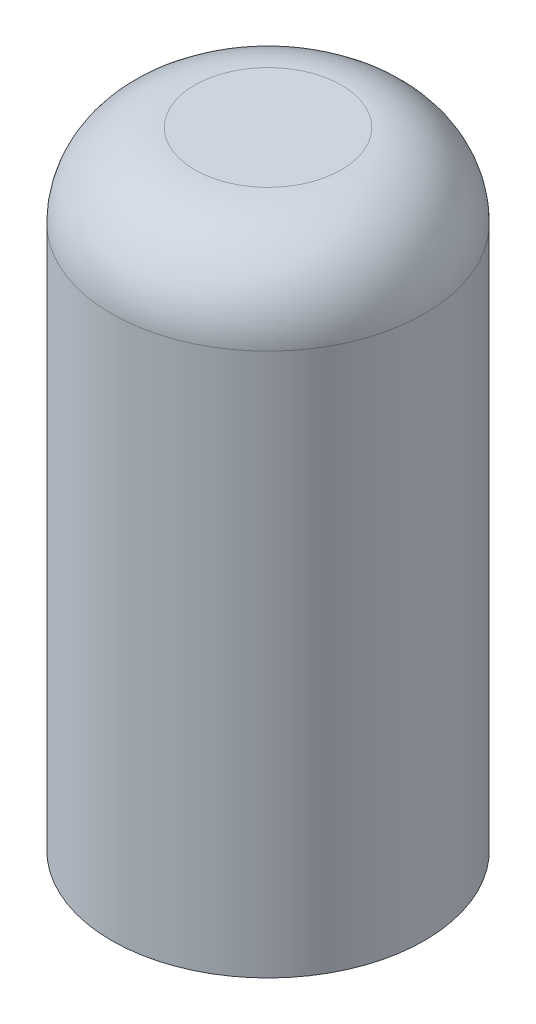
SolidWorks part; units mm, degrees
material "Ti-6Al-4VSolution treated and aged (SS)"
ref_plane "Front Plane" through (0, 0, 0) normal (0, 0, 1) x (1, 0, 0)
ref_plane "Top Plane" through (0, 0, 0) normal (0, 1, 0) x (1, 0, 0)
ref_plane "Right Plane" through (0, 0, 0) normal (1, 0, 0) x (0, 0, -1)
sketch "Sketch1" plane through (0, 0, 0) normal (0, 1, 0) x (1, 0, 0)
  circle A0 centre (0, 0) radius 56.5
extrude "Boss-Extrude1" add sketch "Sketch1" along normal blind 226
fillet "Fillet1" radius 30 1 edges at (0, 226, 56.5)
